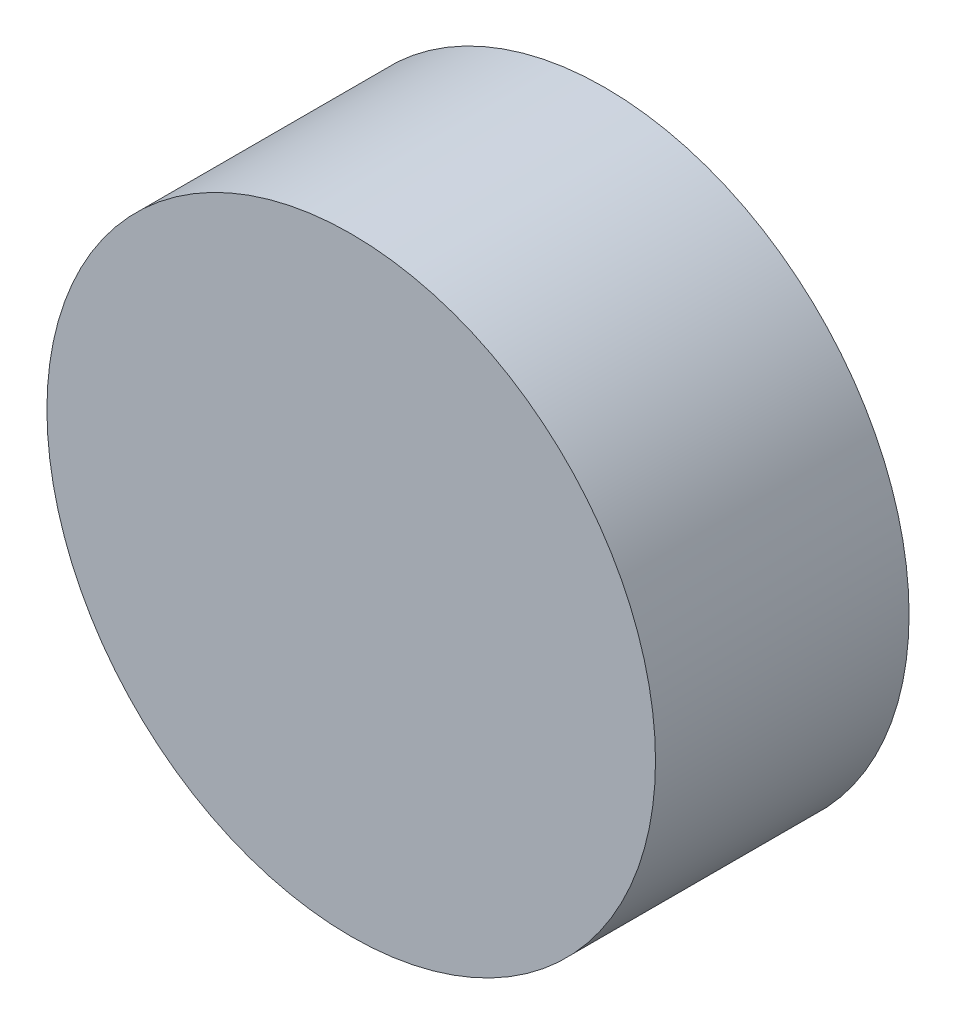
SolidWorks part; units mm, degrees
ref_plane "Front" through (0, 0, 0) normal (0, 0, 1) x (1, 0, 0)
ref_plane "Top" through (0, 0, 0) normal (0, 1, 0) x (1, 0, 0)
ref_plane "Right" through (0, 0, 0) normal (1, 0, 0) x (0, 0, -1)
sketch "Sketch1" plane through (0, 0, 0) normal (0, 0, 1) x (1, 0, 0)
  circle A0 centre (0, 0) radius 3
  dimension "D1" = 6
extrude "Boss-Extrude1" add sketch "Sketch1" along normal blind 2.5
